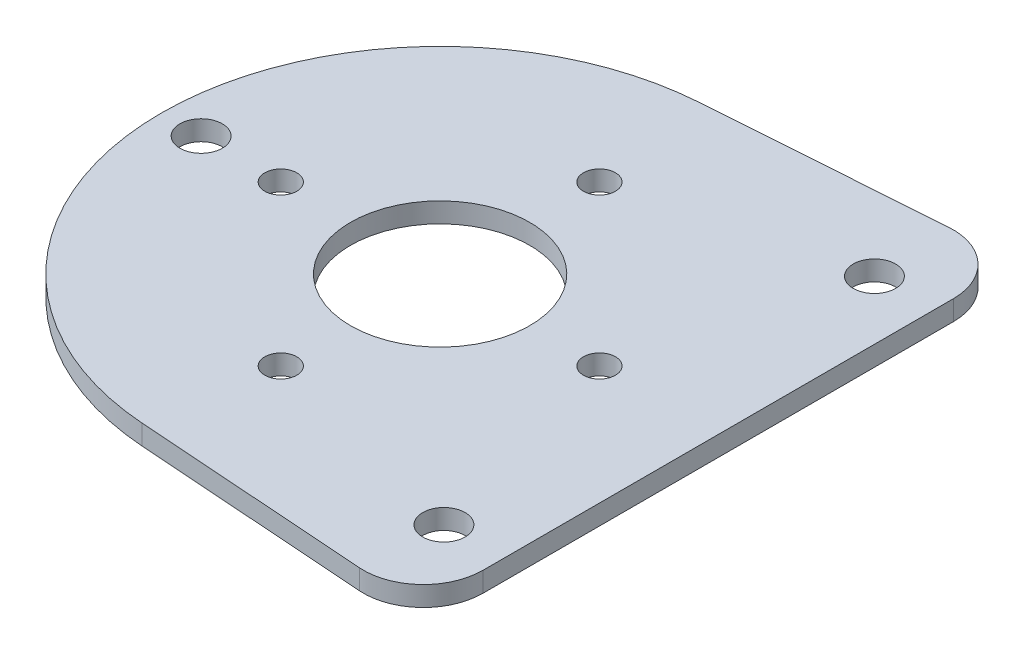
SolidWorks part; units mm, degrees
material "6061 Alloy"
ref_plane "Front Plane" through (0, 0, 0) normal (0, 0, 1) x (1, 0, 0)
ref_plane "Top Plane" through (0, 0, 0) normal (0, 1, 0) x (1, 0, 0)
ref_plane "Right Plane" through (0, 0, 0) normal (1, 0, 0) x (0, 0, -1)
sketch "Sketch1" plane through (0, 0, 0) normal (0, 1, 0) x (1, 0, 0)
  line L0 (87.0156, 23.109) -> (-1.4599, 13.6381) construction
  line L1 (-25.4, 0) -> (0, -25.4) construction
  line L2 (-25.4, 0) -> (0, 25.4) construction
  line L3 (0, 25.4) -> (25.4, 0) construction
  line L4 (0, -25.4) -> (25.4, 0) construction
  line L5 (-25.4, 0) -> (25.4, 0) construction
  line L6 (0, 25.4) -> (0, -25.4) construction
  line L7 (87.0156, -23.109) -> (-1.4599, -13.6381) construction
  line L8 (85.8846, 50.6719) -> (-3.1541, 44.338)
  line L9 (85.8846, -50.6719) -> (-3.1541, -44.338)
  circle A1 centre (0, 0) radius 13.716 construction
  circle A2 centre (89.4893, 0) radius 23.241 construction
  circle A3 centre (89.4893, 0) radius 14.2875
  circle A4 centre (0, 0) radius 14.2812
  arc A5 (-3.1541, 44.338) -> (-3.1541, -44.338) centre (0, 0) ccw
  arc A6 (85.8846, 50.6719) -> (85.8846, -50.6719) centre (89.4893, 0) cw
  point P0 (0, 0)
  point P2 (140.2893, 0)
  point P27 (-44.45, 0)
  dimension "D1" = 50.8
  dimension "D2" = 27.432
  dimension "D3" = 46.482
  dimension "D5" = 28.575
  dimension "D6" = 28.5623
  dimension "D4" = 89.4893
  dimension "D7" = 44.45
  dimension "D8" = 50.8
extrude "Boss-Extrude1" add sketch "Sketch1" along normal blind 3.175
hole_wizard "#10 Clearance Hole1" positions "Sketch2" profile "Sketch3" hole size "#10" standard "ANSI Inch" end condition through all
sketch "Sketch2" plane through (0, 3.175, 0) normal (0, 1, 0) x (1, 0, 0)
  line L0 (-44.45, 0) -> (-14.2811, 0) construction
  arc A0 (-3.1541, 44.338) -> (-3.1541, -44.338) centre (0, 0) ccw construction
  circle A1 centre (0, 0) radius 14.2812 construction
  point P0 (0, 25.4)
  point P3 (25.4, 0)
  point P6 (0, -25.4)
  point P9 (-25.4, 0)
sketch "Sketch3" plane through (0, 3.175, -25.4) normal (1, 0, 0) x (0, 0, 1)
  line L0 (0, 0) -> (0, 3.175)
  line L1 (0, 3.175) -> (2.5527, 3.175)
  line L2 (2.5527, 3.175) -> (2.5527, 0)
  line L5 (2.5527, 0) -> (0, 0)
  line L11 (0, -6.35) -> (0, 107.95) construction
  dimension "Thru Hole Dia." = 5.1054
  dimension "Thru Hole Depth" = 3.175
hole_wizard "1/4 Clearance Hole1" positions "Sketch4" profile "Sketch5" hole size "1/4" standard "ANSI Inch" end condition through all
sketch "Sketch4" plane through (0, 3.175, 0) normal (0, 1, 0) x (1, 0, 0)
  line L0 (-29.3656, 0) -> (126.5098, 0) construction
  line L1 (140.2893, 0) -> (112.7303, 0) construction
  line L2 (-14.2811, 0) -> (-44.45, 0) construction
  line L3 (85.8846, 50.6719) -> (-3.1541, 44.338) construction
  arc A0 (85.8846, -50.6719) -> (85.8846, 50.6719) centre (89.4893, 0) ccw construction
  circle A1 centre (89.4893, 0) radius 23.241 construction
  circle A2 centre (0, 0) radius 14.2812 construction
  arc A3 (-3.1541, 44.338) -> (-3.1541, -44.338) centre (0, 0) ccw construction
  circle A5 centre (89.4893, 0) radius 14.2875 construction
  point P4 (54.5643, 34.925)
  point P6 (54.5643, -34.925)
  point P54 (114.8893, 25.4)
  point P56 (114.8893, -25.4)
  point P62 (-38.1, 0)
  point P65 (34.925, 34.3147)
  point P69 (34.925, -34.3147)
  dimension "D1" = 34.925
  dimension "D3" = 25.4
  dimension "D2" = 25.4
  dimension "D4" = 34.925
  dimension "D5" = 38.1
  dimension "D6" = 34.925
  dimension "D7" = 12.7
sketch "Sketch5" plane through (54.5643, 3.175, -34.925) normal (1, 0, 0) x (0, 0, 1)
  line L0 (0, 0) -> (0, 3.175)
  line L1 (0, 3.175) -> (3.3782, 3.175)
  line L2 (3.3782, 3.175) -> (3.3782, 0)
  line L5 (3.3782, 0) -> (0, 0)
  line L11 (0, -6.35) -> (0, 107.95) construction
  dimension "Thru Hole Dia." = 6.7564
  dimension "Thru Hole Depth" = 3.175
sketch "Sketch6" plane through (0, 3.175, 0) normal (0, 1, 0) x (1, 0, 0)
  line L0 (5.08, 25.4) -> (5.08, 13.3471)
  line L1 (-5.08, 25.4) -> (-5.08, 13.3471)
  line L2 (-25.4, 0) -> (25.4, 0) construction
  line L3 (5.08, -25.4) -> (5.08, -13.3471)
  line L4 (-5.08, -25.4) -> (-5.08, -13.3471)
  arc A0 (-5.08, 25.4) -> (5.08, 25.4) centre (0, 25.4) cw
  circle A1 centre (0, 0) radius 14.2812 construction
  arc A2 (-5.08, 13.3471) -> (5.08, 13.3471) centre (0, 0) cw
  arc A3 (-5.08, -25.4) -> (5.08, -25.4) centre (0, -25.4) ccw
  arc A4 (-5.08, -13.3471) -> (5.08, -13.3471) centre (0, 0) ccw
  circle M7 centre (0, 25.4) radius 2.5527
  circle M9 centre (0, -25.4) radius 2.5527
  circle M16 centre (0, 0) radius 14.2812
  dimension "D1" = 5.08
extrude "Cut-Extrude1" [suppressed] cut sketch "Sketch6" against normal through all contours A0 L1 L0 M16 M7 | L4 A3 L3 M16 M9
fillet "Fillet1" [suppressed] radius 7.62
sketch "Sketch7" plane through (0, 3.175, 0) normal (0, 1, 0) x (1, 0, 0)
  line L0 (44.323, 47.7154) -> (140.2893, 54.5422)
  line L1 (85.8846, 50.6719) -> (-3.1541, 44.338) construction
  line L2 (140.2893, 54.5422) -> (140.2893, -54.5422)
  line L3 (140.2893, -54.5422) -> (44.323, -47.7154)
  line L4 (-3.1541, -44.338) -> (85.8846, -50.6719) construction
  line L5 (44.323, -47.7154) -> (44.323, 47.7154)
  arc A1 (85.8846, -50.6719) -> (85.8846, 50.6719) centre (89.4893, 0) ccw construction
  circle A3 centre (34.925, -34.3147) radius 3.3782 construction
  dimension "D1" = 9.398
extrude "Cut-Extrude2" cut sketch "Sketch7" against normal through all
fillet "Fillet2" radius 9.525 2 edges at (44.323, 1.5875, -47.7154) (44.323, 1.5875, 47.7154)
sketch "Sketch8" [suppressed] plane through (0, 3.175, 0) normal (0, 1, 0) x (1, 0, 0)
  circle A0 centre (0, 0) radius 14.6622
  dimension "D1" = 29.3243
extrude "Cut-Extrude3" [suppressed] cut sketch "Sketch8" against normal through all
